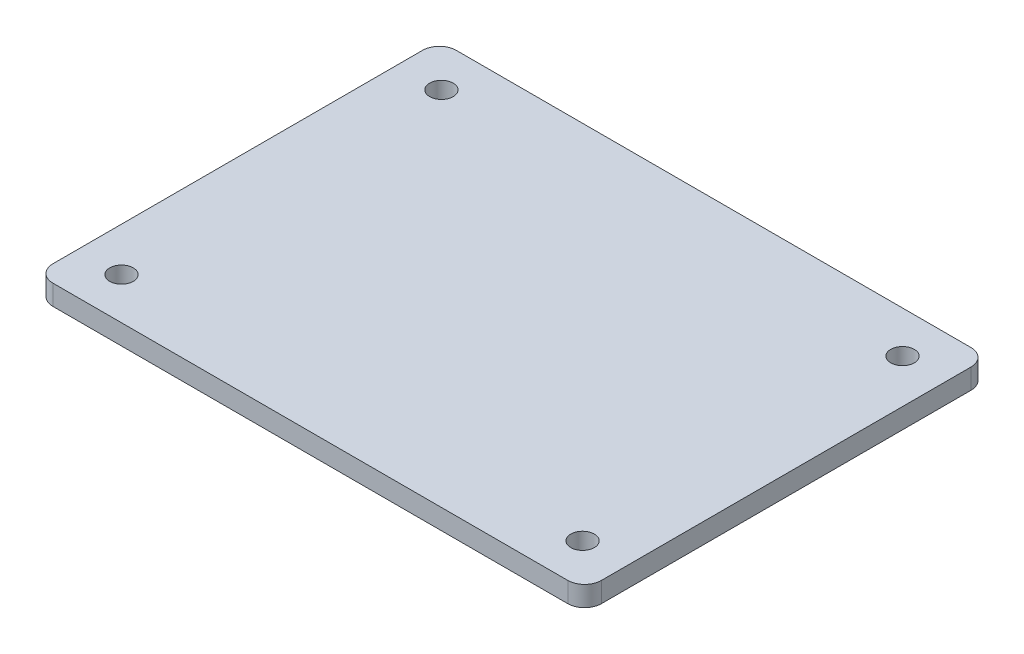
SolidWorks part; units mm, degrees
ref_plane "Alzado" through (0, 0, 0) normal (0, 0, 1) x (1, 0, 0)
ref_plane "Planta" through (0, 0, 0) normal (0, 1, 0) x (1, 0, 0)
ref_plane "Vista lateral" through (0, 0, 0) normal (1, 0, 0) x (0, 0, -1)
sketch "Croquis1" plane through (0, 0, 0) normal (0, 1, 0) x (1, 0, 0)
  line L0 (-1000, 0) -> (49000, 0) construction
  line L1 (-38.3, -30) -> (38.3, -30)
  line L2 (-40.8, -27.5) -> (-40.8, 27.5)
  line L3 (-38.3, 30) -> (38.3, 30)
  line L4 (40.8, -27.5) -> (40.8, 27.5)
  line L5 (-40.8, -30) -> (40.8, 30) construction
  line L6 (-40.8, 30) -> (40.8, -30) construction
  line L7 (0, -1000) -> (0, 49000) construction
  arc A0 (-38.3, -30) -> (-40.8, -27.5) centre (-38.3, -27.5) cw
  arc A1 (38.3, -30) -> (40.8, -27.5) centre (38.3, -27.5) ccw
  arc A2 (38.3, 30) -> (40.8, 27.5) centre (38.3, 27.5) cw
  arc A3 (-40.8, 27.5) -> (-38.3, 30) centre (-38.3, 27.5) cw
  circle A4 centre (-34.3, 23.8) radius 1.75
  circle A5 centre (-34.3, -23.8) radius 1.75
  circle A6 centre (34.3, -23.8) radius 1.75
  circle A7 centre (34.3, 23.8) radius 1.75
  point P0 (0, 0)
  dimension "D3" = 2.5
  dimension "D4" = 3.5
  dimension "D1" = 81.6
  dimension "D2" = 60
  dimension "D5" = 6.5
  dimension "D6" = 6.2
extrude "Saliente-Extruir1" add sketch "Croquis1" along normal blind 3
